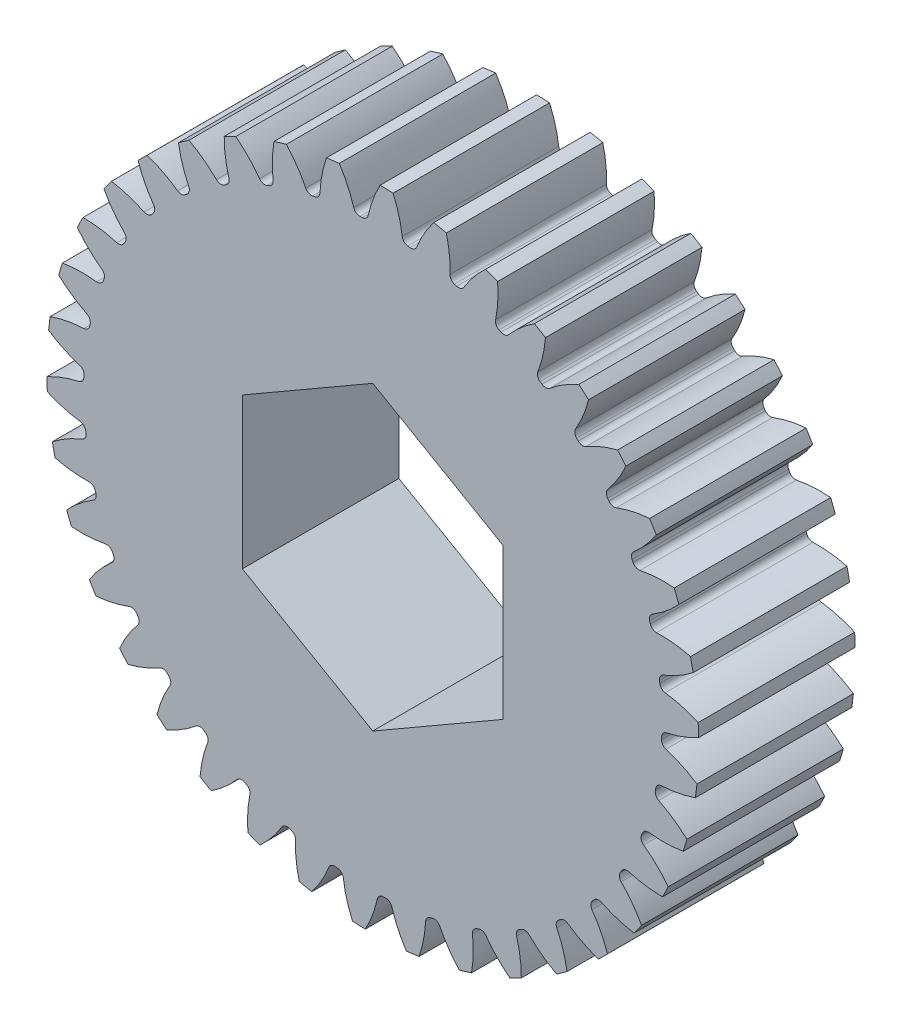
SolidWorks part; units mm, degrees
ref_plane "Front" through (0, 0, 0) normal (0, 0, 1) x (1, 0, 0)
ref_plane "Top" through (0, 0, 0) normal (0, 1, 0) x (1, 0, 0)
ref_plane "Right" through (0, 0, 0) normal (1, 0, 0) x (0, 0, -1)
sketch "Sketch3" plane through (0, 0, 0) normal (0, 0, 1) x (1, 0, 0)
  circle A0 centre (0, 0) radius 15.875
  dimension "od" = 31.75
extrude "gearBody" add sketch "Sketch3" along normal blind 7.62
sketch "Sketch2" plane through (0, 0, 0) normal (0, 0, 1) x (1, 0, 0)
  line L0 (0, 0) -> (13.093, 5.4233) construction
  line L1 (17.6436, -3.6644) -> (0, 0) construction
  line L2 (0, 0) -> (36.3143, 0) construction
  line L3 (15.0812, -0.034) -> (15.0295, -1.2488) construction
  line L5 (15.0553, -0.6414) -> (0, 0) construction
  line L7 (0, 0) -> (14.1717, 0) construction
  arc A0 (14.1689, -0.2844) -> (14.1417, -0.9217) centre (0, 0) ccw construction
  arc A1 (15.8717, 0.3229) -> (15.7867, -1.6717) centre (0, 0) ccw construction
  arc A2 (15.0812, -0.034) -> (15.0295, -1.2488) centre (0, 0) ccw construction
  arc A3 (14.0626, -0.6566) -> (14.0675, -0.5418) centre (0, 0) ccw
  arc A4 (17.6436, -3.6644) -> (14.2775, -0.9613) centre (12.5843, -6.5172) ccw
  arc A5 (17.6436, -3.6644) -> (17.8914, 2.1505) centre (0, 0) ccw
  arc A6 (17.8914, 2.1505) -> (14.3075, -0.2565) centre (13.093, 5.4233) cw
  arc A7 (14.0675, -0.5418) -> (14.3075, -0.2565) centre (14.371, -0.5535) cw
  arc A8 (14.2775, -0.9613) -> (14.0626, -0.6566) centre (14.366, -0.6708) cw
  point P6 (17.8914, 2.1505)
  point P22 (17.6436, -3.6644)
  dimension "baseDia" = 28.3435
  dimension "od" = 31.75
  dimension "pd" = 30.1625
  dimension "rd" = 28.1559
  dimension "rFillet" = 0.3037
  dimension "pointX" = 17.8914
  dimension "pointY" = 2.1505
  dimension "CTT" = 1.2148
  dimension "flankCenterAngle" = 22.5
extrude "toothCut" cut sketch "Sketch2" along normal through all
pattern_circular "CirPattern1" count 38 over 360 about axis through (0, 0, 0) along (0, 0, 1) of "toothCut"
sketch "hub1Dia" plane through (0, 0, 0) normal (0, 0, -1) x (-1, 0, 0)
  circle A0 centre (0, 0) radius 12.7
  dimension "hub1Dia" = 25.4
sketch "hub2Dia" plane through (0, 0, 7.62) normal (0, 0, 1) x (1, 0, 0)
  circle A0 centre (0, 0) radius 12.7
  dimension "hub2dia" = 25.4
sketch "boreDia" plane through (0, 0, 0) normal (0, 0, 1) x (1, 0, 0)
  circle A0 centre (0, 0) radius 3.175
  dimension "boreDia" = 6.35
extrude "bore" cut sketch "boreDia" against normal mid plane 25400
sketch "Sketch4" plane through (0, 0, 0) normal (0, 0, -1) x (-1, 0, 0)
  line L1 (0, 7.3323) -> (-6.35, 3.6662)
  line L2 (-6.35, 3.6662) -> (-6.35, -3.6662)
  line L3 (-6.35, -3.6662) -> (0, -7.3323)
  line L4 (0, -7.3323) -> (6.35, -3.6662)
  line L5 (6.35, -3.6662) -> (6.35, 3.6662)
  line L6 (6.35, 3.6662) -> (0, 7.3323)
  circle A0 centre (0, 0) radius 6.35 construction
  dimension "D1" = 12.7
extrude "Cut-Extrude1" cut sketch "Sketch4" against normal through all
